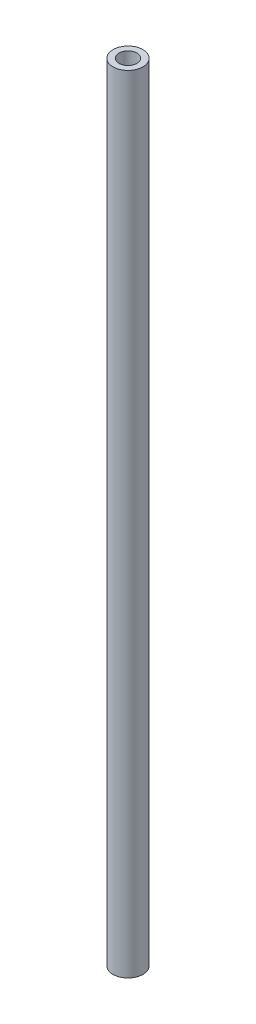
SolidWorks part; units mm, degrees
ref_plane "Front Plane" through (0, 0, 0) normal (0, 0, 1) x (1, 0, 0)
ref_plane "Top Plane" through (0, 0, 0) normal (0, 1, 0) x (1, 0, 0)
ref_plane "Right Plane" through (0, 0, 0) normal (1, 0, 0) x (0, 0, -1)
sketch "Sketch1" plane through (0, 0, 0) normal (0, 1, 0) x (1, 0, 0)
  circle A0 centre (0, 0) radius 2
  circle A1 centre (0, 0) radius 1.2
  dimension "D1" = 4
  dimension "D2" = 2.4
extrude "Boss-Extrude1" add sketch "Sketch1" along normal blind 105
